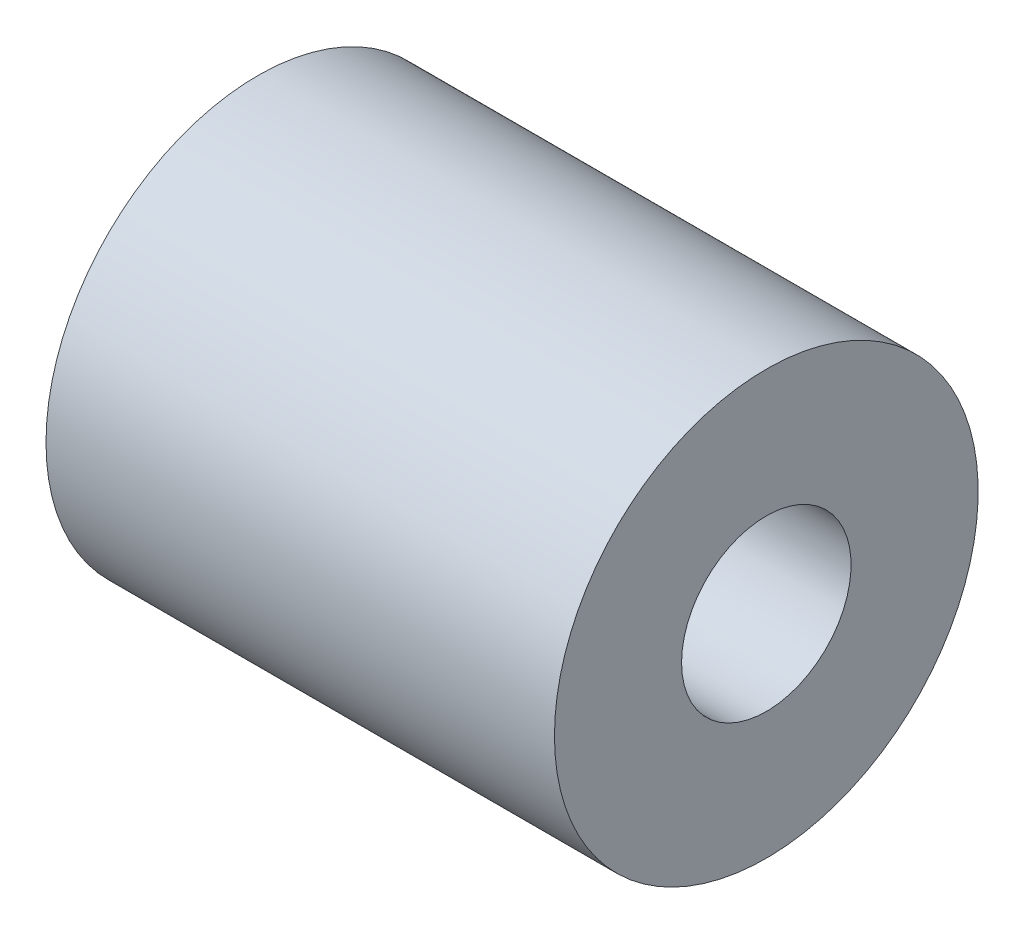
SolidWorks part; units mm, degrees
material "PVC hart"
ref_plane "Ebene vorne" through (0, 0, 0) normal (0, 0, 1) x (1, 0, 0)
ref_plane "Ebene oben" through (0, 0, 0) normal (0, 1, 0) x (1, 0, 0)
ref_plane "Ebene rechts" through (0, 0, 0) normal (1, 0, 0) x (0, 0, -1)
sketch "Skizze1" plane through (0, 0, 0) normal (0, 0, 1) x (1, 0, 0)
  line L0 (-6.4601, 0) -> (6.3568, 0) construction
  line L1 (-6.925, 1) -> (-6, 1.925)
  line L2 (-6, 1.925) -> (-6, 2.5)
  line L3 (0, 2.5) -> (0, 1)
  line L4 (0, 1) -> (-6.925, 1)
  line L5 (-6, 2.5) -> (0, 2.5)
  dimension "D1" = 2
  dimension "D2" = 3.85
  dimension "D3" = 45
  dimension "D4" = 5
  dimension "D5" = 6
revolve "Rotation1" add sketch "Skizze1" angle 360 about L0
